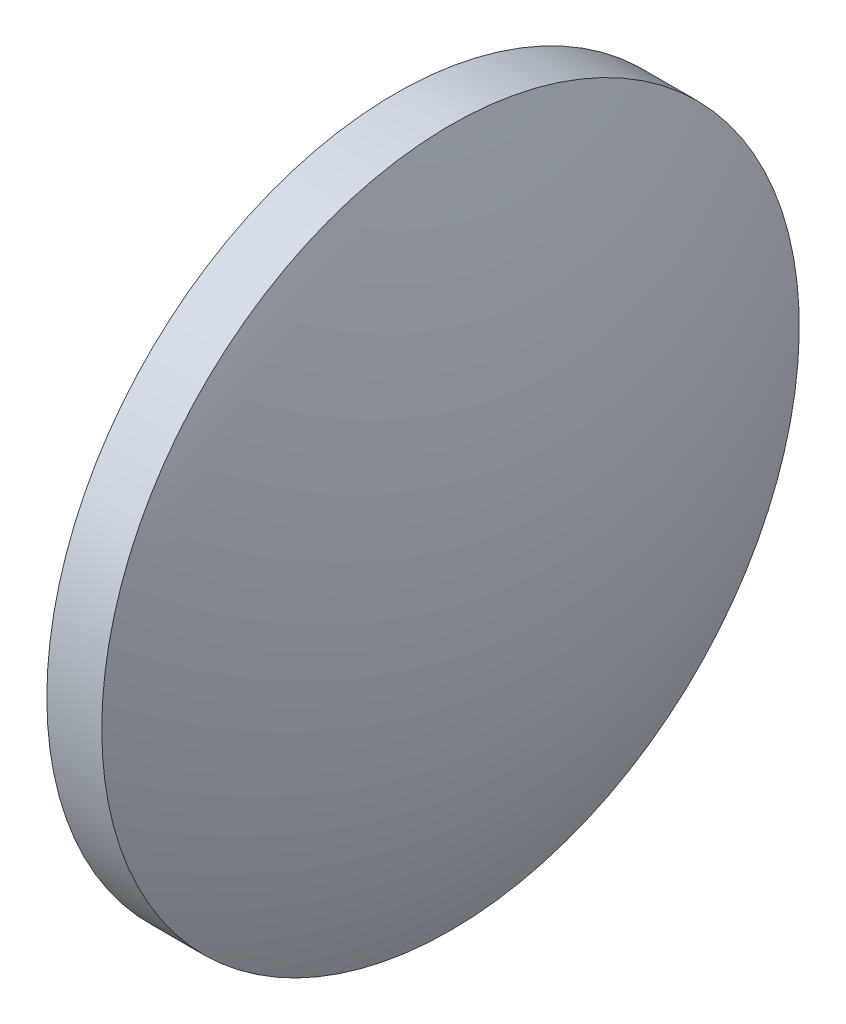
SolidWorks part; units mm, degrees
ref_plane "前视基准面" through (0, 0, 0) normal (0, 0, 1) x (1, 0, 0)
ref_plane "上视基准面" through (0, 0, 0) normal (0, 1, 0) x (1, 0, 0)
ref_plane "右视基准面" through (0, 0, 0) normal (1, 0, 0) x (0, 0, -1)
sketch "草图1" plane through (0, 0, 0) normal (0, 0, 1) x (1, 0, 0)
  line L0 (429.3069, 143.1477) -> (448.1029, 143.1477) construction
  line L1 (435.0451, 143.1477) -> (435.0451, 155.8477)
  line L2 (435.0451, 155.8477) -> (437.0451, 155.8477)
  line L3 (439.6451, 143.1477) -> (435.0451, 143.1477)
  arc A0 (439.6451, 143.1477) -> (437.0451, 155.8477) centre (407.3278, 143.1477) ccw
revolve "旋转1" add sketch "草图1" angle 360 about L0
